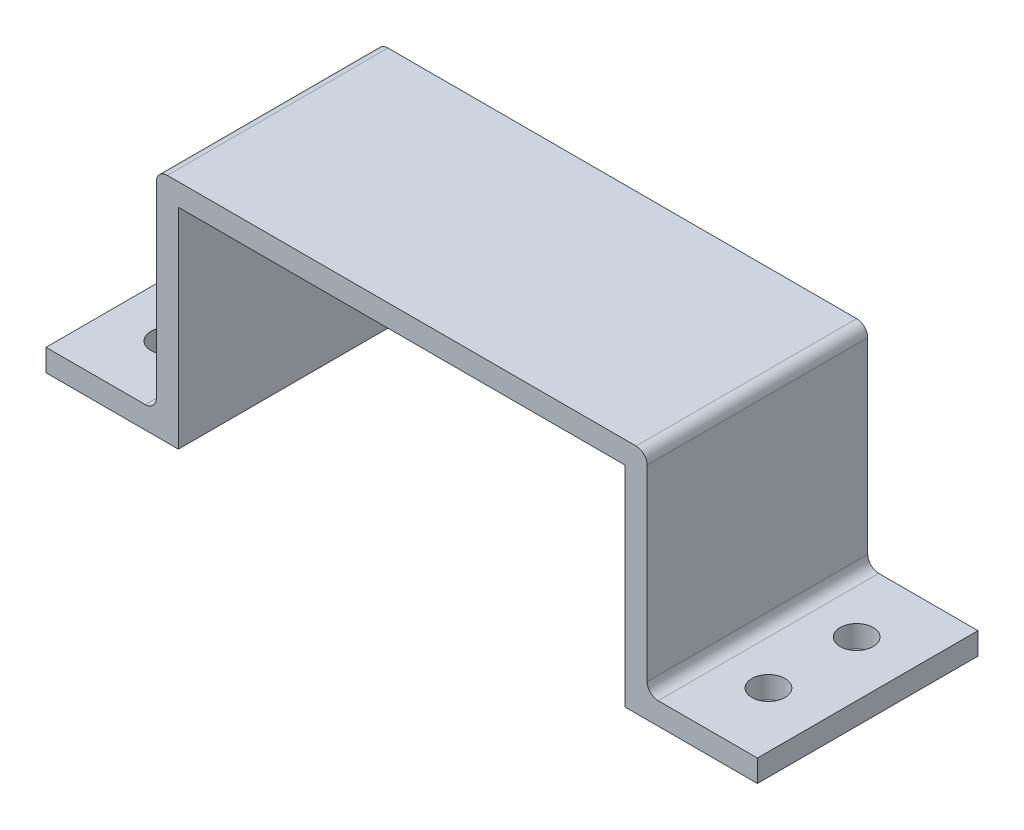
SolidWorks part; units mm, degrees
ref_plane "Front Plane" through (0, 0, 0) normal (0, 0, 1) x (1, 0, 0)
ref_plane "Top Plane" through (0, 0, 0) normal (0, 1, 0) x (1, 0, 0)
ref_plane "Right Plane" through (0, 0, 0) normal (1, 0, 0) x (0, 0, -1)
sketch "Sketch2" plane through (0, 0, 0) normal (0, 0, 1) x (1, 0, 0)
  line L0 (-283.1871, 0) -> (13876.1681, 0) construction
  line L1 (0, -283.1871) -> (0, 13876.1681) construction
  line L2 (0, 21) -> (0, 19) construction
  line L3 (-20.25, 19) -> (20.25, 19)
  line L4 (20.25, 19) -> (20.25, 0)
  line L5 (20.25, 0) -> (32.25, 0)
  line L6 (32.25, 0) -> (32.25, 2)
  line L7 (32.25, 2) -> (22.25, 2)
  line L8 (22.25, 2) -> (22.25, 21)
  line L9 (22.25, 21) -> (-22.25, 21)
  line L10 (-32.25, 0) -> (-32.25, 2)
  line L11 (-32.25, 2) -> (-22.25, 2)
  line L12 (-20.25, 0) -> (-32.25, 0)
  line L13 (-20.25, 19) -> (-20.25, 0)
  line L14 (-22.25, 2) -> (-22.25, 21)
  dimension "D1" = 2
  dimension "D2" = 20.25
  dimension "D3" = 22.25
  dimension "D4" = 2
  dimension "D5" = 19
  dimension "D6" = 12
extrude "Boss-Extrude1" add sketch "Sketch2" along normal blind 20
sketch "Sketch3" plane through (0, 2, 0) normal (0, 1, 0) x (1, 0, 0)
  line L0 (32.25, -20) -> (32.25, 0) construction
  line L1 (32.25, 0) -> (22.25, 0) construction
  line L2 (32.25, -20) -> (22.25, -20) construction
  line L3 (0, 0) -> (0, -20) construction
  line L4 (22.25, -20) -> (-22.25, -20) construction
  circle A0 centre (27.25, -6) radius 1.5
  circle A1 centre (27.25, -14) radius 1.5
  circle A2 centre (-27.25, -14) radius 1.5
  circle A3 centre (-27.25, -6) radius 1.5
  dimension "D1" = 3
  dimension "D2" = 5
  dimension "D3" = 6
  dimension "D4" = 6
  dimension "D5" = 5
extrude "Cut-Extrude1" cut sketch "Sketch3" against normal through all
fillet "Fillet1" radius 1 4 edges at (-22.25, 2, 10) (-22.25, 21, 10) (22.25, 2, 10) (22.25, 21, 10)
